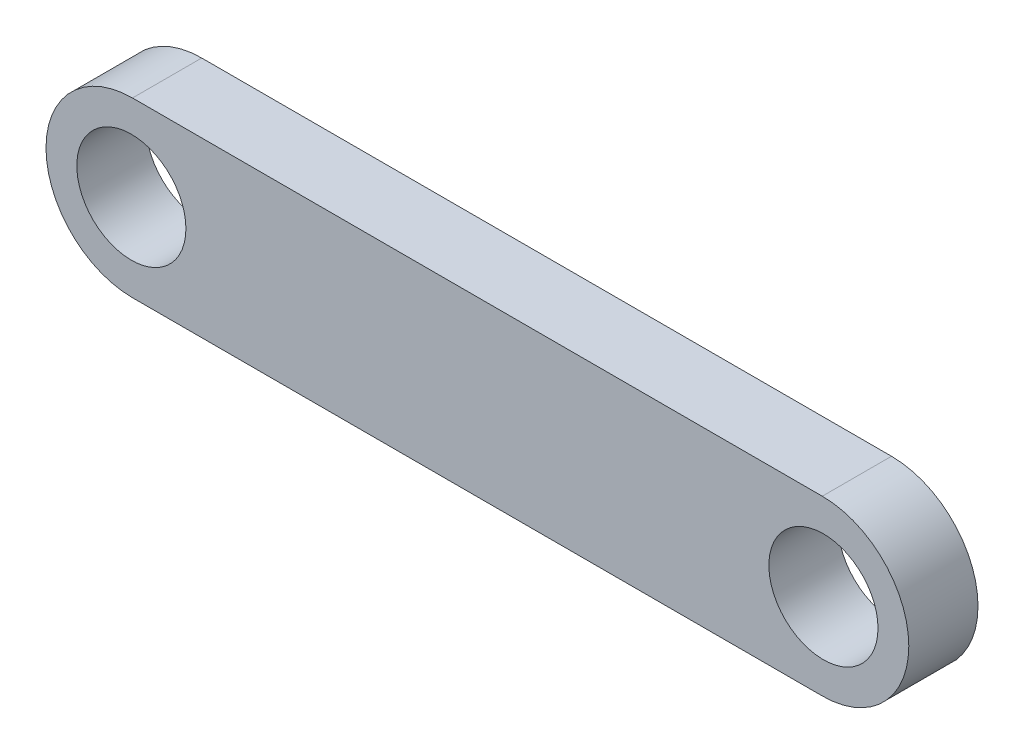
SolidWorks part; units mm, degrees
material "Acrylic (Medium-high impact)"
ref_plane "Front Plane" through (0, 0, 0) normal (0, 0, 1) x (1, 0, 0)
ref_plane "Top Plane" through (0, 0, 0) normal (0, 1, 0) x (1, 0, 0)
ref_plane "Right Plane" through (0, 0, 0) normal (1, 0, 0) x (0, 0, -1)
sketch "Sketch1" plane through (0, 0, 0) normal (0, 0, 1) x (1, 0, 0)
  line L0 (0, 0) -> (30, 0) construction
  line L1 (0, 3) -> (30, 3)
  line L2 (0, -3) -> (30, -3)
  arc A0 (0, 3) -> (0, -3) centre (0, 0) ccw
  arc A1 (30, -3) -> (30, 3) centre (30, 0) ccw
  circle A2 centre (0, 0) radius 2.395
  circle A3 centre (30, 0) radius 2.395
  point P3 (15, 0)
  dimension "D1" = 3
  dimension "D3" = 4.79
  dimension "D2" = 30
extrude "Boss-Extrude1" add sketch "Sketch1" along normal blind 3
sketch "Sketch2" plane through (0, 0, 3) normal (0, 0, 1) x (1, 0, 0)
  line L0 (15, 3) -> (15, -3) construction
  line L1 (30, 3) -> (0, 3) construction
  line L2 (0, -3) -> (30, -3) construction
  line L3 (0.05, 0) -> (29.95, 0) construction
  line L4 (0.05, 3.75) -> (29.95, 3.75)
  line L5 (0.05, -3.75) -> (29.95, -3.75)
  line L6 (30, 0) -> (33.7, 0) construction
  arc A0 (0.05, 3.75) -> (0.05, -3.75) centre (0.05, 0) ccw
  arc A1 (29.95, -3.75) -> (29.95, 3.75) centre (29.95, 0) ccw
  circle A2 centre (0, 0) radius 2.365
  circle A3 centre (30, 0) radius 2.365
  point P8 (15, 0)
  dimension "D2" = 4.73
  dimension "D1" = 3.7
  dimension "D4" = 7.5
extrude "Boss-Extrude2" add sketch "Sketch2" against normal up to surface (3 mm away) up to face at (15, 0, 0)
